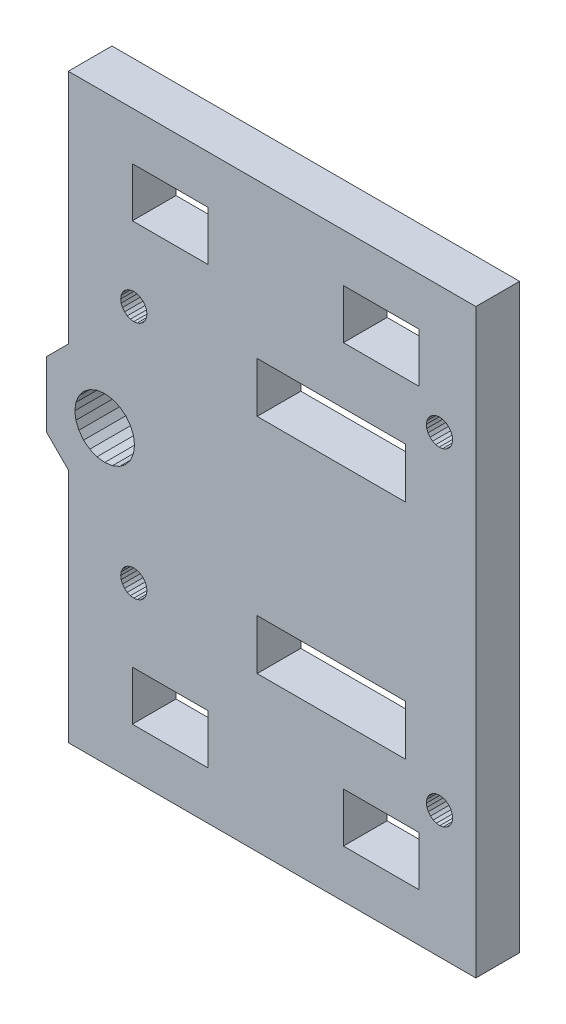
SolidWorks part; units mm, degrees
material "Maple"
ref_plane "Front Plane" through (0, 0, 0) normal (0, 0, 1) x (1, 0, 0)
ref_plane "Top Plane" through (0, 0, 0) normal (0, 1, 0) x (1, 0, 0)
ref_plane "Right Plane" through (0, 0, 0) normal (1, 0, 0) x (0, 0, -1)
sketch "Sketch1" plane through (0, 0, 0) normal (0, 0, 1) x (1, 0, 0)
  line L826 (-451.4117, -88.0132) -> (-507.4117, -88.0132)
  line L827 (-481.4627, -146.7132) -> (-481.4627, -139.8132)
  line L828 (-498.3117, -127.9632) -> (-498.4514, -126.902)
  line L829 (-500.3617, -131.5139) -> (-499.5125, -130.8623)
  line L830 (-502.4117, -132.0632) -> (-501.3505, -131.9234)
  line L831 (-503.4728, -131.9234) -> (-502.4117, -132.0632)
  line L832 (-505.3108, -130.8623) -> (-504.4617, -131.5139)
  line L833 (-505.9624, -130.0132) -> (-505.3108, -130.8623)
  line L834 (-506.372, -126.902) -> (-506.5117, -127.9632)
  line L835 (-505.9624, -125.9132) -> (-506.372, -126.902)
  line L836 (-505.3108, -125.064) -> (-505.9624, -125.9132)
  line L837 (-504.4617, -124.4124) -> (-505.3108, -125.064)
  line L838 (-461.0942, -139.8132) -> (-461.0942, -146.7132)
  line L839 (-501.3505, -124.0029) -> (-502.4117, -123.8632)
  line L840 (-499.5125, -125.064) -> (-500.3617, -124.4124)
  line L841 (-499.9705, -110.6132) -> (-500.1503, -111.0473)
  line L842 (-500.1503, -111.0473) -> (-500.2117, -111.5132)
  line L843 (-500.2117, -111.5132) -> (-500.1503, -111.979)
  line L844 (-500.1503, -111.979) -> (-499.9705, -112.4132)
  line L845 (-458.1602, -105.8904) -> (-457.9901, -106.3284)
  line L846 (-457.9901, -106.3284) -> (-457.7123, -106.7074)
  line L847 (-457.7123, -106.7074) -> (-457.346, -107.0017)
  line L848 (-457.346, -107.0017) -> (-456.9159, -107.1911)
  line L849 (-456.9159, -107.1911) -> (-456.4515, -107.2627)
  line L850 (-456.4515, -107.2627) -> (-455.9844, -107.2117)
  line L851 (-455.9844, -107.2117) -> (-455.5464, -107.0416)
  line L852 (-455.5464, -107.0416) -> (-455.1674, -106.7638)
  line L853 (-455.1674, -106.7638) -> (-454.8731, -106.3975)
  line L854 (-488.2117, -161.3132) -> (-488.2117, -154.5132)
  line L855 (-498.6117, -154.5132) -> (-488.2117, -154.5132)
  line L856 (-498.6117, -161.3132) -> (-498.6117, -154.5132)
  line L857 (-488.2117, -161.3132) -> (-498.6117, -161.3132)
  line L858 (-488.2117, -101.4132) -> (-488.2117, -94.6132)
  line L859 (-498.6117, -94.6132) -> (-488.2117, -94.6132)
  line L860 (-498.6117, -101.4132) -> (-498.6117, -94.6132)
  line L861 (-488.2117, -101.4132) -> (-498.6117, -101.4132)
  line L862 (-499.9705, -112.4132) -> (-499.6844, -112.7859)
  line L863 (-499.6844, -112.7859) -> (-499.3117, -113.072)
  line L864 (-499.3117, -113.072) -> (-498.8775, -113.2518)
  line L865 (-498.8775, -113.2518) -> (-498.4117, -113.3132)
  line L866 (-498.4117, -113.3132) -> (-497.9458, -113.2518)
  line L867 (-481.4627, -109.2132) -> (-461.0942, -109.2132)
  line L868 (-481.4627, -116.1132) -> (-461.0942, -116.1132)
  line L869 (-481.4627, -139.8132) -> (-461.0942, -139.8132)
  line L870 (-481.4627, -146.7132) -> (-461.0942, -146.7132)
  line L871 (-455.5464, -148.8847) -> (-455.9844, -148.7146)
  line L872 (-455.9844, -148.7146) -> (-456.4515, -148.6636)
  line L873 (-456.4515, -148.6636) -> (-456.9159, -148.7352)
  line L874 (-456.9159, -148.7352) -> (-457.346, -148.9246)
  line L875 (-457.346, -148.9246) -> (-457.7123, -149.2189)
  line L876 (-457.7123, -149.2189) -> (-457.9901, -149.5979)
  line L877 (-457.9901, -149.5979) -> (-458.1602, -150.0359)
  line L878 (-498.861, -125.9132) -> (-499.5125, -125.064)
  line L879 (-498.4514, -126.902) -> (-498.861, -125.9132)
  line L880 (-510.4117, -132.4522) -> (-507.4117, -135.4522)
  line L881 (-510.4117, -123.4741) -> (-510.4117, -132.4522)
  line L882 (-510.4117, -123.4741) -> (-507.4117, -120.4741)
  line L883 (-507.4117, -120.4741) -> (-507.4117, -88.0132)
  line L884 (-500.3617, -124.4124) -> (-501.3505, -124.0029)
  line L885 (-502.4117, -123.8632) -> (-503.4728, -124.0029)
  line L886 (-503.4728, -124.0029) -> (-504.4617, -124.4124)
  line L887 (-506.5117, -127.9632) -> (-506.372, -129.0243)
  line L888 (-506.372, -129.0243) -> (-505.9624, -130.0132)
  line L889 (-504.4617, -131.5139) -> (-503.4728, -131.9234)
  line L890 (-501.3505, -131.9234) -> (-500.3617, -131.5139)
  line L891 (-499.5125, -130.8623) -> (-498.861, -130.0132)
  line L892 (-498.861, -130.0132) -> (-498.4514, -129.0243)
  line L893 (-498.4514, -129.0243) -> (-498.3117, -127.9632)
  line L894 (-461.0942, -109.2132) -> (-461.0942, -116.1132)
  line L895 (-481.4627, -116.1132) -> (-481.4627, -109.2132)
  line L896 (-454.8731, -106.3975) -> (-454.6837, -105.9674)
  line L897 (-454.6837, -105.9674) -> (-454.6121, -105.503)
  line L898 (-454.6121, -105.503) -> (-454.6631, -105.0359)
  line L899 (-454.6631, -105.0359) -> (-454.8333, -104.5979)
  line L900 (-454.8333, -104.5979) -> (-455.111, -104.2189)
  line L901 (-455.111, -104.2189) -> (-455.4773, -103.9246)
  line L902 (-455.4773, -103.9246) -> (-455.9074, -103.7352)
  line L903 (-455.9074, -103.7352) -> (-456.3718, -103.6636)
  line L904 (-456.3718, -103.6636) -> (-456.8389, -103.7146)
  line L905 (-456.8389, -103.7146) -> (-457.2769, -103.8847)
  line L906 (-457.2769, -103.8847) -> (-457.6559, -104.1625)
  line L907 (-457.6559, -104.1625) -> (-457.9502, -104.5288)
  line L908 (-457.9502, -104.5288) -> (-458.1396, -104.9589)
  line L909 (-458.1396, -104.9589) -> (-458.2112, -105.4233)
  line L910 (-451.4117, -88.0132) -> (-451.4117, -167.9132)
  line L911 (-507.4117, -167.9132) -> (-507.4117, -135.4522)
  line L912 (-451.4117, -167.9132) -> (-507.4117, -167.9132)
  line L913 (-469.6117, -154.5132) -> (-459.2117, -154.5132)
  line L914 (-459.2117, -154.5132) -> (-459.2117, -161.3132)
  line L915 (-459.2117, -161.3132) -> (-469.6117, -161.3132)
  line L916 (-469.6117, -161.3132) -> (-469.6117, -154.5132)
  line L917 (-469.6117, -94.6132) -> (-459.2117, -94.6132)
  line L918 (-459.2117, -94.6132) -> (-459.2117, -101.4132)
  line L919 (-459.2117, -101.4132) -> (-469.6117, -101.4132)
  line L920 (-469.6117, -101.4132) -> (-469.6117, -94.6132)
  line L921 (-499.6844, -110.2404) -> (-499.9705, -110.6132)
  line L922 (-499.3117, -109.9543) -> (-499.6844, -110.2404)
  line L923 (-498.8775, -109.7745) -> (-499.3117, -109.9543)
  line L924 (-498.4117, -109.7132) -> (-498.8775, -109.7745)
  line L925 (-497.9458, -109.7745) -> (-498.4117, -109.7132)
  line L926 (-497.5117, -109.9543) -> (-497.9458, -109.7745)
  line L927 (-497.1389, -110.2404) -> (-497.5117, -109.9543)
  line L928 (-496.8528, -110.6132) -> (-497.1389, -110.2404)
  line L929 (-496.673, -111.0473) -> (-496.8528, -110.6132)
  line L930 (-496.6117, -111.5132) -> (-496.673, -111.0473)
  line L931 (-496.673, -111.979) -> (-496.6117, -111.5132)
  line L932 (-496.8528, -112.4132) -> (-496.673, -111.979)
  line L933 (-497.1389, -112.7859) -> (-496.8528, -112.4132)
  line L934 (-497.5117, -113.072) -> (-497.1389, -112.7859)
  line L935 (-497.9458, -113.2518) -> (-497.5117, -113.072)
  line L936 (-458.2112, -105.4233) -> (-458.1602, -105.8904)
  line L937 (-499.9705, -143.5132) -> (-500.1503, -143.9473)
  line L938 (-499.6844, -143.1404) -> (-499.9705, -143.5132)
  line L939 (-499.3117, -142.8543) -> (-499.6844, -143.1404)
  line L940 (-498.8775, -142.6745) -> (-499.3117, -142.8543)
  line L941 (-498.4117, -142.6132) -> (-498.8775, -142.6745)
  line L942 (-497.9458, -142.6745) -> (-498.4117, -142.6132)
  line L943 (-497.5117, -142.8543) -> (-497.9458, -142.6745)
  line L944 (-497.1389, -143.1404) -> (-497.5117, -142.8543)
  line L945 (-496.8528, -143.5132) -> (-497.1389, -143.1404)
  line L946 (-496.673, -143.9473) -> (-496.8528, -143.5132)
  line L947 (-496.6117, -144.4132) -> (-496.673, -143.9473)
  line L948 (-496.673, -144.879) -> (-496.6117, -144.4132)
  line L949 (-496.8528, -145.3132) -> (-496.673, -144.879)
  line L950 (-497.1389, -145.6859) -> (-496.8528, -145.3132)
  line L951 (-497.5117, -145.972) -> (-497.1389, -145.6859)
  line L952 (-497.9458, -146.1518) -> (-497.5117, -145.972)
  line L953 (-498.4117, -146.2132) -> (-497.9458, -146.1518)
  line L954 (-498.8775, -146.1518) -> (-498.4117, -146.2132)
  line L955 (-499.3117, -145.972) -> (-498.8775, -146.1518)
  line L956 (-499.6844, -145.6859) -> (-499.3117, -145.972)
  line L957 (-499.9705, -145.3132) -> (-499.6844, -145.6859)
  line L958 (-500.1503, -144.879) -> (-499.9705, -145.3132)
  line L959 (-500.2117, -144.4132) -> (-500.1503, -144.879)
  line L960 (-500.1503, -143.9473) -> (-500.2117, -144.4132)
  line L961 (-458.1602, -150.0359) -> (-458.2112, -150.503)
  line L962 (-455.1674, -149.1625) -> (-455.5464, -148.8847)
  line L963 (-454.8731, -149.5288) -> (-455.1674, -149.1625)
  line L964 (-454.6837, -149.9589) -> (-454.8731, -149.5288)
  line L965 (-454.6121, -150.4233) -> (-454.6837, -149.9589)
  line L966 (-454.6631, -150.8904) -> (-454.6121, -150.4233)
  line L967 (-454.8333, -151.3284) -> (-454.6631, -150.8904)
  line L968 (-455.111, -151.7074) -> (-454.8333, -151.3284)
  line L969 (-455.4773, -152.0017) -> (-455.111, -151.7074)
  line L970 (-455.9074, -152.1911) -> (-455.4773, -152.0017)
  line L971 (-456.3718, -152.2627) -> (-455.9074, -152.1911)
  line L972 (-456.8389, -152.2117) -> (-456.3718, -152.2627)
  line L973 (-457.2769, -152.0416) -> (-456.8389, -152.2117)
  line L974 (-457.6559, -151.7638) -> (-457.2769, -152.0416)
  line L975 (-457.9502, -151.3975) -> (-457.6559, -151.7638)
  line L976 (-458.1396, -150.9674) -> (-457.9502, -151.3975)
  line L977 (-458.2112, -150.503) -> (-458.1396, -150.9674)
  line L8810 (-486.9114, -125.0256) -> (-487.9916, -125.0256)
  line L8811 (-487.9916, -125.0256) -> (-485.8499, -125.0256)
  line L8812 (-485.8499, -125.0256) -> (-486.9114, -125.0256)
  line L8813 (-486.9114, -125.0256) -> (-486.9114, -129.3335)
  line L8814 (-486.9114, -129.3335) -> (-486.9114, -125.0256)
extrude "Boss-Extrude1" add sketch "Sketch1" along normal blind 6
